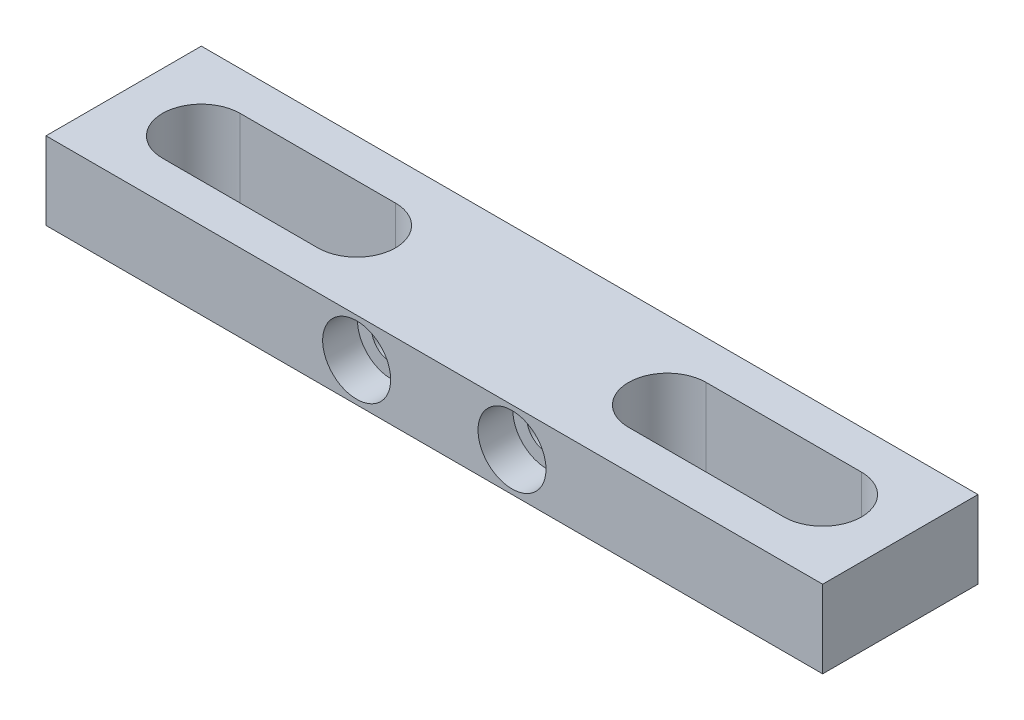
SolidWorks part; units mm, degrees
material "6061 Alloy"
ref_plane "Front Plane" through (0, 0, 0) normal (0, 0, 1) x (1, 0, 0)
ref_plane "Top Plane" through (0, 0, 0) normal (0, 1, 0) x (1, 0, 0)
ref_plane "Right Plane" through (0, 0, 0) normal (1, 0, 0) x (0, 0, -1)
sketch "Sketch2" plane through (0, 0, 0) normal (0, 1, 0) x (1, 0, 0)
  line L1 (-10.8558, 8.8418) -> (52.6442, 8.8418)
  line L2 (-10.8558, 8.8418) -> (-10.8558, -3.8582)
  line L3 (-10.8558, -3.8582) -> (52.6442, -3.8582)
  line L4 (52.6442, 8.8418) -> (52.6442, -3.8582)
  dimension "D1" = 12.7
  dimension "D2" = 63.5
extrude "Boss-Extrude1" add sketch "Sketch2" along normal blind 6.35
hole_wizard "CBORE for #4 Socket Head Cap Screw1" positions "Sketch6" profile "Sketch5" counterbore size "#4" standard "ANSI Inch" end condition through all
sketch "Sketch6" plane through (0, 0, 3.8582) normal (0, 0, 1) x (1, 0, 0)
  line L0 (-10.8558, 6.35) -> (-10.8558, 0) construction
  line L1 (-10.8558, 0) -> (52.6442, 0) construction
  point P0 (14.5442, 3.175)
  point P2 (27.2442, 3.175)
  dimension "D1" = 12.7
  dimension "D2" = 25.4
  dimension "D3" = 3.175
  dimension "D4" = 3.175
sketch "Sketch5" plane through (14.5442, 3.175, 3.8582) normal (1, 0, 0) x (0, -1, 0)
  line L0 (0, 0) -> (0, 12.7)
  line L1 (0, 12.7) -> (1.6319, 12.7)
  line L3 (1.6319, 12.7) -> (1.632, 2.8448)
  line L4 (1.632, 2.8448) -> (2.7788, 2.8448)
  line L5 (2.7788, 2.8448) -> (2.7788, 0)
  line L7 (2.7788, 0) -> (0, 0)
  line L11 (0, -6.35) -> (0, 107.95) construction
  dimension "Thru Hole Dia." = 3.2639
  dimension "Thru Hole Depth" = 12.7
  dimension "C'Bore Dia." = 5.5575
  dimension "C'Bore Depth" = 2.8448
sketch "Sketch8" plane through (0, 6.35, 0) normal (0, 1, 0) x (1, 0, 0)
  line L0 (-4.5058, 2.4918) -> (8.1942, 2.4918) construction
  line L1 (-4.5058, 5.6668) -> (8.1942, 5.6668)
  line L2 (-4.5058, -0.6832) -> (8.1942, -0.6832)
  line L3 (33.5942, 2.4918) -> (46.2942, 2.4918) construction
  line L4 (33.5942, 5.6668) -> (46.2942, 5.6668)
  line L5 (33.5942, -0.6832) -> (46.2942, -0.6832)
  line L6 (-10.8558, -3.8582) -> (52.6442, -3.8582) construction
  line L7 (-10.8558, 8.8418) -> (-10.8558, -3.8582) construction
  line L8 (52.6442, -3.8582) -> (52.6442, 8.8418) construction
  arc A0 (-4.5058, 5.6668) -> (-4.5058, -0.6832) centre (-4.5058, 2.4918) ccw
  arc A1 (8.1942, -0.6832) -> (8.1942, 5.6668) centre (8.1942, 2.4918) ccw
  arc A2 (33.5942, 5.6668) -> (33.5942, -0.6832) centre (33.5942, 2.4918) ccw
  arc A3 (46.2942, -0.6832) -> (46.2942, 5.6668) centre (46.2942, 2.4918) ccw
  point P2 (1.8442, 2.4918)
  point P7 (39.9442, 2.4918)
  dimension "D6" = 6.35
  dimension "D1" = 6.35
  dimension "D2" = 6.35
  dimension "D3" = 6.35
  dimension "D4" = 12.7
  dimension "D5" = 12.7
  dimension "D7" = 6.35
extrude "Cut-Extrude1" cut sketch "Sketch8" against normal through all
